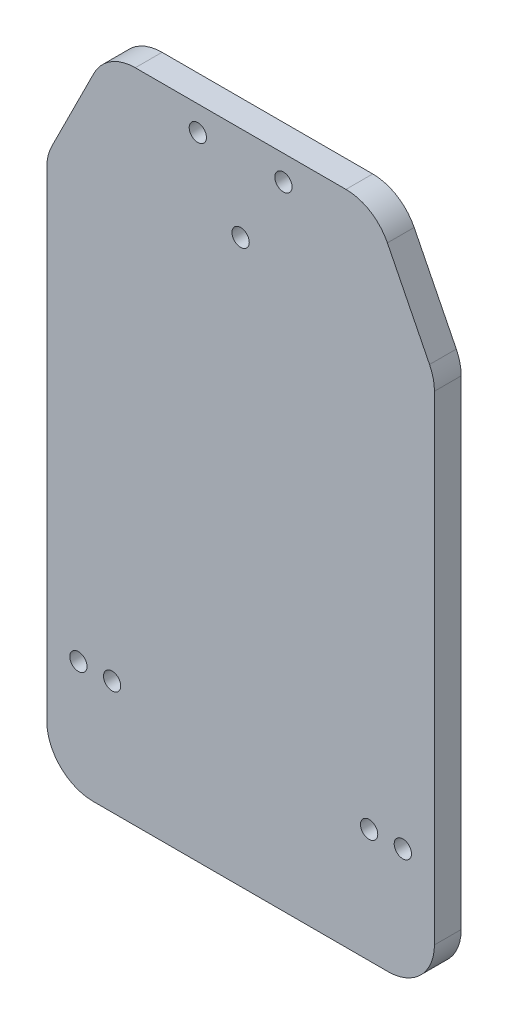
SolidWorks part; units mm, degrees
material "Teak"
ref_plane "Front Plane" through (0, 0, 0) normal (0, 0, 1) x (1, 0, 0)
ref_plane "Top Plane" through (0, 0, 0) normal (0, 1, 0) x (1, 0, 0)
ref_plane "Right Plane" through (0, 0, 0) normal (1, 0, 0) x (0, 0, -1)
sketch "Sketch1" plane through (0, 0, 0) normal (0, 0, 1) x (1, 0, 0)
  line L0 (55, 153.8) -> (30, 153.8) construction
  line L1 (12.1115, 142.7443) -> (2.1115, 122.7443) construction
  line L2 (0, 113.8) -> (0, 0) construction
  line L7 (55, 153.8) -> (55, -20) construction
  line L8 (20, -20) -> (90, -20) construction
  line L9 (110, 113.8) -> (110, 0) construction
  line L10 (97.8885, 142.7443) -> (107.8885, 122.7443) construction
  line L11 (55, 153.8) -> (80, 153.8) construction
  line L12 (55, 144.8) -> (30, 144.8)
  line L13 (20.1613, 138.7193) -> (10.1613, 118.7193)
  line L14 (9, 113.8) -> (9, 0)
  line L15 (20, -11) -> (90, -11)
  line L16 (101, 113.8) -> (101, 0)
  line L17 (89.8387, 138.7193) -> (99.8387, 118.7193)
  line L18 (55, 144.8) -> (80, 144.8)
  line L21 (80, 166.9) -> (30, 166.9) construction
  line L22 (10, -33.1) -> (100, -33.1) construction
  arc A0 (0, 0) -> (20, -20) centre (20, 0) ccw construction
  arc A1 (2.1115, 122.7443) -> (0, 113.8) centre (20, 113.8) ccw construction
  arc A2 (30, 153.8) -> (12.1115, 142.7443) centre (30, 133.8) ccw construction
  arc A6 (80, 153.8) -> (97.8885, 142.7443) centre (80, 133.8) cw construction
  arc A7 (107.8885, 122.7443) -> (110, 113.8) centre (90, 113.8) cw construction
  arc A8 (110, 0) -> (90, -20) centre (90, 0) cw construction
  arc A9 (30, 144.8) -> (20.1613, 138.7193) centre (30, 133.8) ccw
  arc A10 (10.1613, 118.7193) -> (9, 113.8) centre (20, 113.8) ccw
  arc A11 (9, 0) -> (20, -11) centre (20, 0) ccw
  arc A12 (101, 0) -> (90, -11) centre (90, 0) cw
  arc A13 (99.8387, 118.7193) -> (101, 113.8) centre (90, 113.8) cw
  arc A14 (80, 144.8) -> (89.8387, 138.7193) centre (80, 133.8) cw
  point P10 (42.5, 153.8)
  point P20 (65.7684, -20)
  dimension "D1" = 20
  dimension "D2" = 40
  dimension "D3" = 25
  dimension "D4" = 110
  dimension "D5" = 173.8
  dimension "D7" = 200
  dimension "D6" = 9
extrude "Boss-Extrude1" add sketch "Sketch1" along normal blind 6.35 contours L12 A9 L13 A10 L14 A11 L15 A12 L16 A13 L17 A14 L18
sketch "Sketch2" plane through (0, 0, 6.35) normal (0, 0, 1) x (1, 0, 0)
  circle A0 centre (16.5, 16) radius 2.05
  circle A1 centre (24.5, 16) radius 2.05
  circle A2 centre (85.5, 16) radius 2.05
  circle A3 centre (93.5, 16) radius 2.05
  circle A4 centre (44.84, 138.8985) radius 2.05
  circle A5 centre (55, 122.4282) radius 2.05
  circle A6 centre (65.16, 138.8985) radius 2.05
  dimension "D1" = 4.1
  dimension "D2" = 4.1
extrude "Cut-Extrude1" cut sketch "Sketch2" against normal up to surface (6.35 mm away) up to face at (55, 84.0376, 0)
